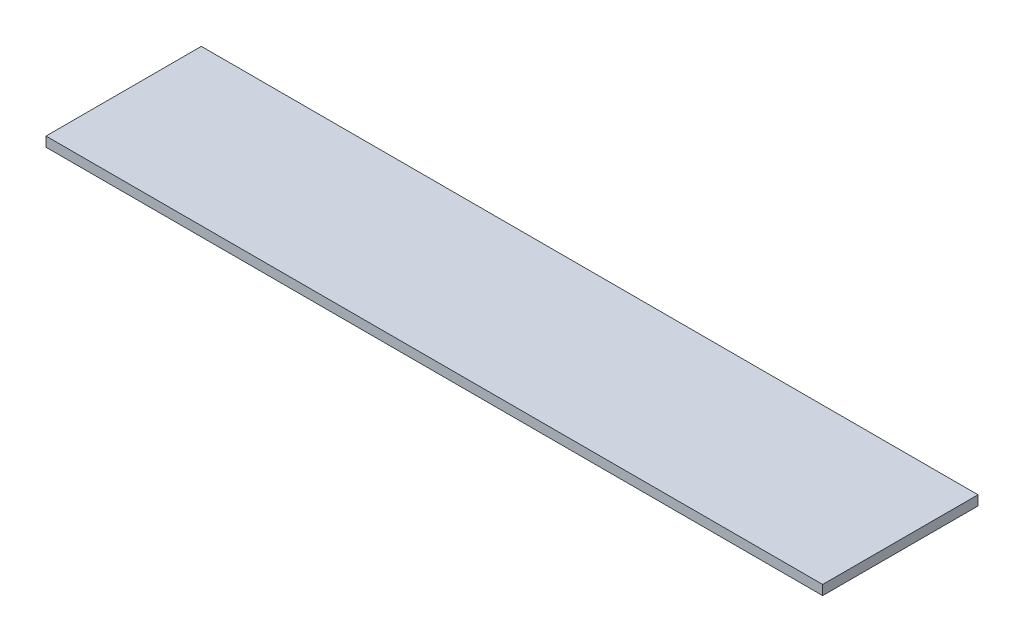
SolidWorks part; units mm, degrees
material "Nylon 101"
ref_plane "Front Plane" through (0, 0, 0) normal (0, 0, 1) x (1, 0, 0)
ref_plane "Top Plane" through (0, 0, 0) normal (0, 1, 0) x (1, 0, 0)
ref_plane "Right Plane" through (0, 0, 0) normal (1, 0, 0) x (0, 0, -1)
sketch "Sketch2" plane through (0, 0, 0) normal (0, 1, 0) x (1, 0, 0)
  line L1 (0, 0) -> (127, 0)
  line L2 (0, 0) -> (0, 25.4)
  line L3 (0, 25.4) -> (127, 25.4)
  line L4 (127, 0) -> (127, 25.4)
  dimension "D1" = 25.4
  dimension "D2" = 127
extrude "Boss-Extrude1" add sketch "Sketch2" along normal blind 1.5875
